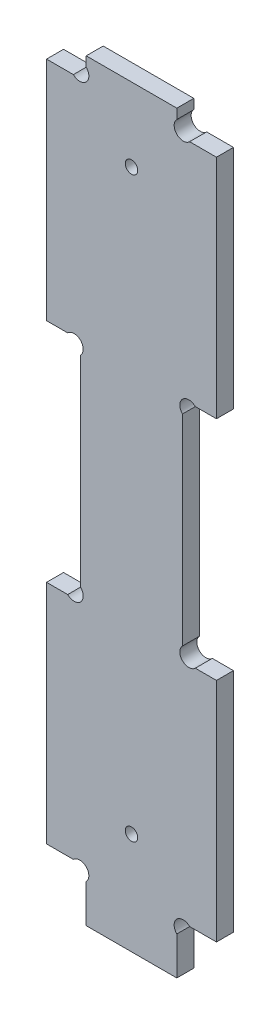
SolidWorks part; units mm, degrees
ref_plane "Plan de face" through (0, 0, 0) normal (0, 0, 1) x (1, 0, 0)
ref_plane "Plan de dessus" through (0, 0, 0) normal (0, 1, 0) x (1, 0, 0)
ref_plane "Plan de droite" through (0, 0, 0) normal (1, 0, 0) x (0, 0, -1)
sketch "Esquisse1" plane through (0, 0, 0) normal (0, 0, 1) x (1, 0, 0)
  line L14 (25.2627, 9) -> (30, 9)
  line L16 (30, 49) -> (30, 9)
  line L17 (26.2627, 49) -> (30, 49)
  line L18 (25.2627, 129) -> (30, 129)
  line L19 (30, 89) -> (30, 129)
  line L20 (26.2627, 89) -> (30, 89)
  line L21 (3.7373, 89) -> (0, 89)
  line L22 (0, 89) -> (0, 129)
  line L23 (4.7373, 129) -> (0, 129)
  line L24 (3.7373, 49) -> (0, 49)
  line L25 (0, 49) -> (0, 9)
  line L26 (4.7373, 9) -> (0, 9)
  line L27 (23, 131.2627) -> (23, 133)
  line L28 (23, 6.7373) -> (23, 0)
  line L29 (24, 86.7373) -> (24, 51.2627)
  line L30 (7, 131.2627) -> (7, 133)
  line L31 (6, 86.7373) -> (6, 51.2627)
  line L32 (7, 6.7373) -> (7, 0)
  line L33 (7, 133) -> (23, 133)
  line L34 (7, 0) -> (23, 0)
  arc A1 (25.2627, 9) -> (23, 6.7373) centre (24.1314, 7.8686) ccw
  arc A2 (24, 51.2627) -> (26.2627, 49) centre (25.1314, 50.1314) ccw
  arc A3 (25.2627, 129) -> (23, 131.2627) centre (24.1314, 130.1314) cw
  arc A5 (24, 86.7373) -> (26.2627, 89) centre (25.1314, 87.8686) cw
  arc A6 (6, 86.7373) -> (3.7373, 89) centre (4.8686, 87.8686) ccw
  arc A8 (4.7373, 129) -> (7, 131.2627) centre (5.8686, 130.1314) ccw
  arc A9 (6, 51.2627) -> (3.7373, 49) centre (4.8686, 50.1314) cw
  arc A10 (4.7373, 9) -> (7, 6.7373) centre (5.8686, 7.8686) cw
  dimension "D13" = 6
  dimension "D14" = 30
  dimension "D20" = 1.6
  dimension "D1" = 40
  dimension "D2" = 40
  dimension "D3" = 40
  dimension "D4" = 4
  dimension "D5" = 9
  dimension "D6" = 30
  dimension "D7" = 16
  dimension "D8" = 18
  dimension "D9" = 16
  dimension "D10" = 7
  dimension "D11" = 7
  dimension "D12" = 6
  dimension "D15" = 1.1314
  dimension "D16" = 1.1314
  dimension "D17" = 2.2627
  dimension "D18" = 2.2627
  dimension "D19" = 7
  dimension "D21" = 1.1314
  dimension "D22" = 1.1314
  dimension "D23" = 2.2627
  dimension "D24" = 2.2627
  dimension "D25" = 1.1314
  dimension "D26" = 2.2627
  dimension "D27" = 2.2627
  dimension "D28" = 1.1314
  dimension "D29" = 1.1314
  dimension "D30" = 1.1314
  dimension "D31" = 2.2627
  dimension "D32" = 2.2627
extrude "Extrusion1" add sketch "Esquisse1" along normal blind 3
sketch "Esquisse2" plane through (0, 0, 3) normal (0, 0, 1) x (1, 0, 0)
  line L0 (25.2627, 9) -> (30, 9) construction
  line L1 (7, 0) -> (23, 0) construction
  line L2 (4.7373, 129) -> (0, 129) construction
  circle A0 centre (15, 18) radius 1.1
  circle A1 centre (15, 120) radius 1.1
  point P4 (15, 0)
  dimension "D2" = 2.2
  dimension "D1" = 9
  dimension "D3" = 9
extrude "Enlèv. mat.-Extru.1" cut sketch "Esquisse2" against normal through all
